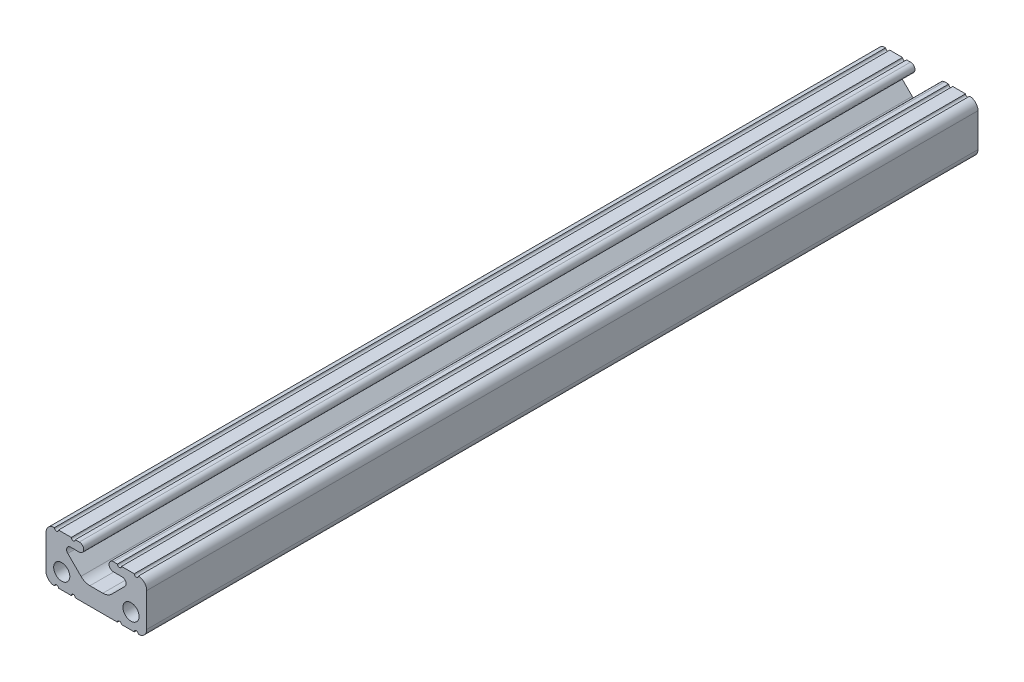
SolidWorks part; units mm, degrees
ref_plane "Front" through (0, 0, 0) normal (0, 0, 1) x (1, 0, 0)
ref_plane "Top" through (0, 0, 0) normal (0, 1, 0) x (1, 0, 0)
ref_plane "Right" through (0, 0, 0) normal (1, 0, 0) x (0, 0, -1)
sketch "Sketch1" plane through (0, 0, 0) normal (0, 0, 1) x (1, 0, 0)
  line L0 (-3.1974, 11.5951) -> (3.1974, 11.5951) construction
  line L1 (-7.504, 9.4742) -> (7.504, 9.4742) construction
  line L28 (-12.7, 10.5918) -> (-12.7, 2.1082)
  line L29 (-9.5504, 0) -> (-6.3246, 0)
  line L30 (-5.3086, 0) -> (5.3086, 0)
  line L31 (6.3246, 0) -> (9.5504, 0)
  line L32 (12.7, 2.1082) -> (12.7, 10.5918)
  line L33 (9.5504, 12.7) -> (6.3246, 12.7)
  line L34 (5.3086, 12.7) -> (4.3023, 12.7)
  line L35 (4.3023, 10.4902) -> (6.488, 10.4902)
  line L36 (7.2064, 8.7558) -> (3.8763, 5.4257)
  line L37 (1.6313, 4.4958) -> (-1.6313, 4.4958)
  line L38 (-3.8763, 5.4257) -> (-7.2064, 8.7558)
  line L39 (-6.488, 10.4902) -> (-4.3023, 10.4902)
  line L40 (-4.3023, 12.7) -> (-5.3086, 12.7)
  line L41 (-6.3246, 12.7) -> (-9.5504, 12.7)
  circle A0 centre (-8.7312, 3.9624) radius 2.032
  circle A1 centre (8.7312, 3.9624) radius 2.032
  arc A36 (-12.7, 2.1082) -> (-10.5791, 0) centre (-10.5918, 2.1082) ccw
  arc A37 (-9.5504, 0) -> (-10.5791, 0) centre (-10.0648, -0.0064) ccw
  arc A38 (-5.3086, 0) -> (-6.3246, 0) centre (-5.8166, 0) ccw
  arc A39 (6.3246, 0) -> (5.3086, 0) centre (5.8166, 0) ccw
  arc A40 (10.5791, 0) -> (9.5504, 0) centre (10.0648, -0.0064) ccw
  arc A41 (10.5791, 0) -> (12.7, 2.1082) centre (10.5918, 2.1082) ccw
  arc A42 (12.7, 10.5918) -> (10.5791, 12.7) centre (10.5918, 10.5918) ccw
  arc A43 (9.5504, 12.7) -> (10.5791, 12.7) centre (10.0648, 12.7063) ccw
  arc A44 (5.3086, 12.7) -> (6.3246, 12.7) centre (5.8166, 12.7) ccw
  arc A45 (4.3023, 12.7) -> (4.3023, 10.4902) centre (4.3023, 11.5951) ccw
  arc A46 (7.2064, 8.7558) -> (6.488, 10.4902) centre (6.488, 9.4742) ccw
  arc A47 (1.6313, 4.4958) -> (3.8763, 5.4257) centre (1.6313, 7.6708) ccw
  arc A48 (-3.8763, 5.4257) -> (-1.6313, 4.4958) centre (-1.6313, 7.6708) ccw
  arc A49 (-6.488, 10.4902) -> (-7.2064, 8.7558) centre (-6.488, 9.4742) ccw
  arc A50 (-4.3023, 10.4902) -> (-4.3023, 12.7) centre (-4.3023, 11.5951) ccw
  arc A51 (-6.3246, 12.7) -> (-5.3086, 12.7) centre (-5.8166, 12.7) ccw
  arc A52 (-10.5791, 12.7) -> (-9.5504, 12.7) centre (-10.0648, 12.7063) ccw
  arc A53 (-10.5791, 12.7) -> (-12.7, 10.5918) centre (-10.5918, 10.5918) ccw
extrude "Boss-Extrude1" add sketch "Sketch1" along normal mid plane 609.6
sketch "Sketch2" plane through (0, 0, -304.8) normal (0, 0, -1) x (-1, 0, 0)
  line L1 (-18.7175, 22.123) -> (24.1656, 22.123)
  line L2 (-18.7175, 22.123) -> (-18.7175, -12.3345)
  line L3 (-18.7175, -12.3345) -> (24.1656, -12.3345)
  line L4 (24.1656, 22.123) -> (24.1656, -12.3345)
extrude "Cut-Extrude1" cut sketch "Sketch2" against normal blind 400
